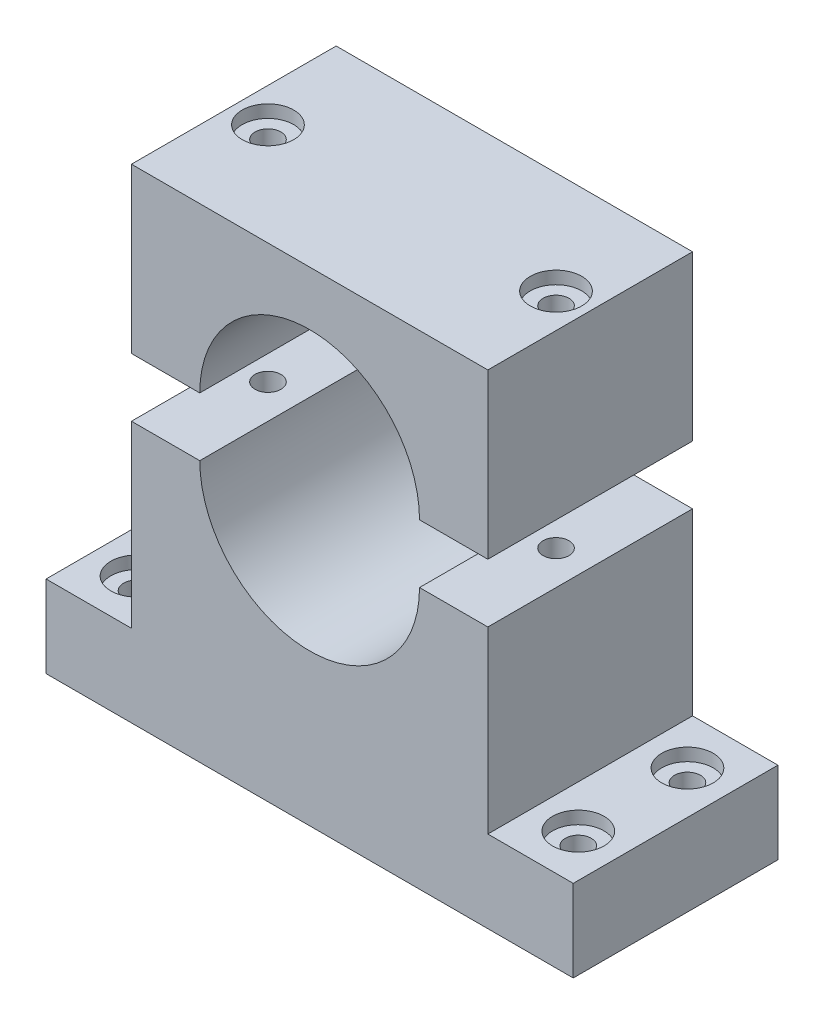
SolidWorks part; units mm, degrees
ref_plane "Front" through (0, 0, 0) normal (0, 0, 1) x (1, 0, 0)
ref_plane "Top" through (0, 0, 0) normal (0, 1, 0) x (1, 0, 0)
ref_plane "Right" through (0, 0, 0) normal (1, 0, 0) x (0, 0, -1)
sketch "Sketch1" plane through (0, 0, 0) normal (0, 0, 1) x (1, 0, 0)
  line L0 (0, 0) -> (-10.0121, 0)
  line L1 (-10.0121, 0) -> (-10.0121, -26.2816)
  line L2 (-10.0121, -26.2816) -> (-22.5271, -26.2816)
  line L3 (-22.5271, -26.2816) -> (-22.5271, -38.2961)
  line L4 (-22.5271, -38.2961) -> (54.7326, -38.2961)
  line L5 (16.1027, -38.2961) -> (16.1027, -16.1027) construction
  line L6 (54.7326, -26.2816) -> (54.7326, -38.2961)
  line L7 (42.2175, -26.2816) -> (54.7326, -26.2816)
  line L8 (42.2175, 0) -> (42.2175, -26.2816)
  line L9 (32.2054, 0) -> (42.2175, 0)
  line L10 (0, 8.5937) -> (-10.0121, 8.5937)
  line L11 (-10.0121, 8.5937) -> (-10.0121, 32.6226)
  line L12 (-10.0121, 32.6226) -> (42.2175, 32.6226)
  line L13 (42.2175, 32.6226) -> (42.2175, 8.5937)
  line L14 (42.2175, 8.5937) -> (32.2054, 8.5937)
  arc A0 (0, 0) -> (32.2054, 0) centre (16.1027, 0) ccw
  arc A1 (0, 8.5937) -> (32.2054, 8.5937) centre (16.1027, 8.5937) cw
  dimension "D1" = 77.2597
  dimension "D6" = 32.6226
  dimension "D3" = 16.1027
  dimension "D2" = 38.2961
  dimension "D4" = 42.2175
  dimension "D7" = 26.2816
extrude "Boss-Extrude1" add sketch "Sketch1" along normal blind 30
hole_wizard "CBORE for #6 Button Head Cap Screw1" positions "Sketch2" profile "Sketch3" counterbore size "#6" standard "ANSI Inch" end condition through all
sketch "Sketch2" plane through (0, 32.6226, 0) normal (0, 1, 0) x (1, 0, 0)
  line L0 (-10.0121, -15) -> (0, -15) construction
  line L1 (-10.0121, -30) -> (-10.0121, 0) construction
  line L2 (0, -30) -> (0, 0) construction
  line L3 (0, -15) -> (32.2054, -15) construction
  line L4 (32.2054, -30) -> (32.2054, 0) construction
  line L5 (32.2054, -15) -> (42.2175, -15) construction
  line L6 (42.2175, -30) -> (42.2175, 0) construction
  point P18 (-5.006, -15)
  point P20 (37.2115, -15)
sketch "Sketch3" plane through (37.2115, 32.6226, 15) normal (1, 0, 0) x (0, 0, 1)
  line L0 (0, 0) -> (0, 70.9187)
  line L1 (0, 70.9187) -> (1.8986, 70.9187)
  line L3 (1.8986, 70.9187) -> (1.8987, 1.8542)
  line L4 (1.8987, 1.8542) -> (3.7706, 1.8542)
  line L5 (3.7706, 1.8542) -> (3.7706, 0)
  line L7 (3.7706, 0) -> (0, 0)
  line L11 (0, -6.35) -> (0, 107.95) construction
  dimension "Thru Hole Dia." = 3.7973
  dimension "Thru Hole Depth" = 70.9187
  dimension "C'Bore Dia." = 7.5413
  dimension "C'Bore Depth" = 1.8542
hole_wizard "CBORE for #6 Button Head Cap Screw2" positions "Sketch4" profile "Sketch5" counterbore size "#6" standard "ANSI Inch" end condition through all
sketch "Sketch4" plane through (0, -26.2816, 0) normal (0, 1, 0) x (1, 0, 0)
  line L0 (-16.2696, 0) -> (-16.2696, -30) construction
  line L1 (-10.0121, 0) -> (-22.5271, 0) construction
  line L2 (-10.0121, -30) -> (-22.5271, -30) construction
  line L5 (16.1027, 0) -> (16.1027, -30) construction
  line L6 (42.2175, 0) -> (-10.0121, 0) construction
  line L7 (42.2175, -30) -> (-10.0121, -30) construction
  point P19 (-16.2696, -7)
  point P21 (-16.2696, -23)
  point P23 (48.475, -23)
  point P24 (48.475, -7)
  dimension "D1" = 7
  dimension "D2" = 7
sketch "Sketch5" plane through (48.475, -26.2816, 7) normal (1, 0, 0) x (0, 0, 1)
  line L0 (0, 0) -> (0, 12.0145)
  line L1 (0, 12.0145) -> (1.8986, 12.0145)
  line L3 (1.8986, 12.0145) -> (1.8987, 1.8542)
  line L4 (1.8987, 1.8542) -> (3.7706, 1.8542)
  line L5 (3.7706, 1.8542) -> (3.7706, 0)
  line L7 (3.7706, 0) -> (0, 0)
  line L11 (0, -6.35) -> (0, 107.95) construction
  dimension "Thru Hole Dia." = 3.7973
  dimension "Thru Hole Depth" = 12.0145
  dimension "C'Bore Dia." = 7.5413
  dimension "C'Bore Depth" = 1.8542
